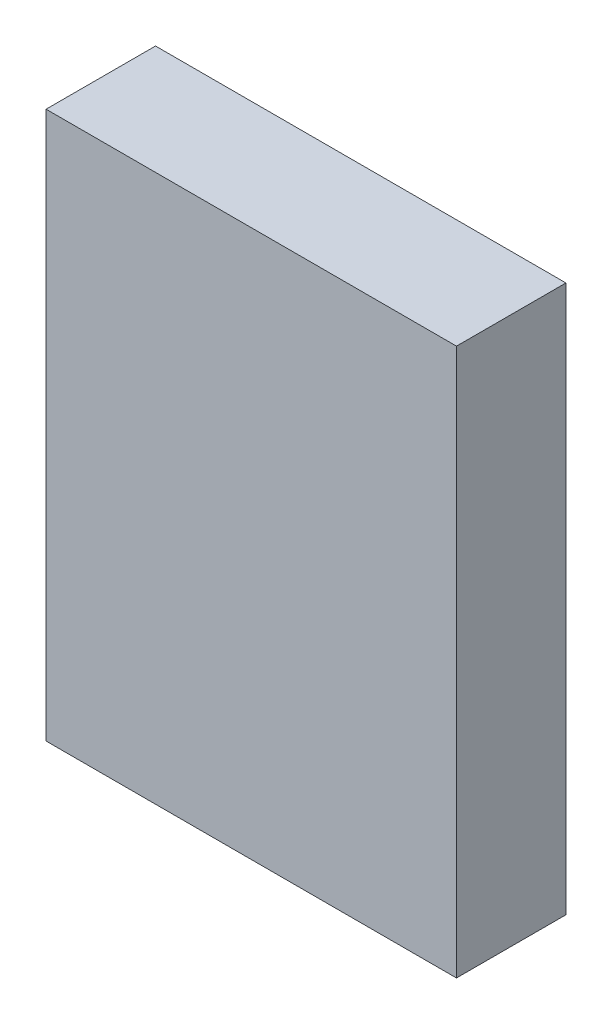
SolidWorks part; units mm, degrees
ref_plane "Front Plane" through (0, 0, 0) normal (0, 0, 1) x (1, 0, 0)
ref_plane "Top Plane" through (0, 0, 0) normal (0, 1, 0) x (1, 0, 0)
ref_plane "Right Plane" through (0, 0, 0) normal (1, 0, 0) x (0, 0, -1)
sketch "Sketch1" plane through (0, 0, 0) normal (0, 0, 1) x (1, 0, 0)
  line L1 (-15, 20) -> (15, 20)
  line L2 (-15, 20) -> (-15, -20)
  line L3 (-15, -20) -> (15, -20)
  line L4 (15, 20) -> (15, -20)
  line L5 (-15, 20) -> (15, -20) construction
  line L6 (-15, -20) -> (15, 20) construction
  point P0 (0, 0)
  dimension "D1" = 40
  dimension "D2" = 30
extrude "Boss-Extrude1" add sketch "Sketch1" along normal blind 8
